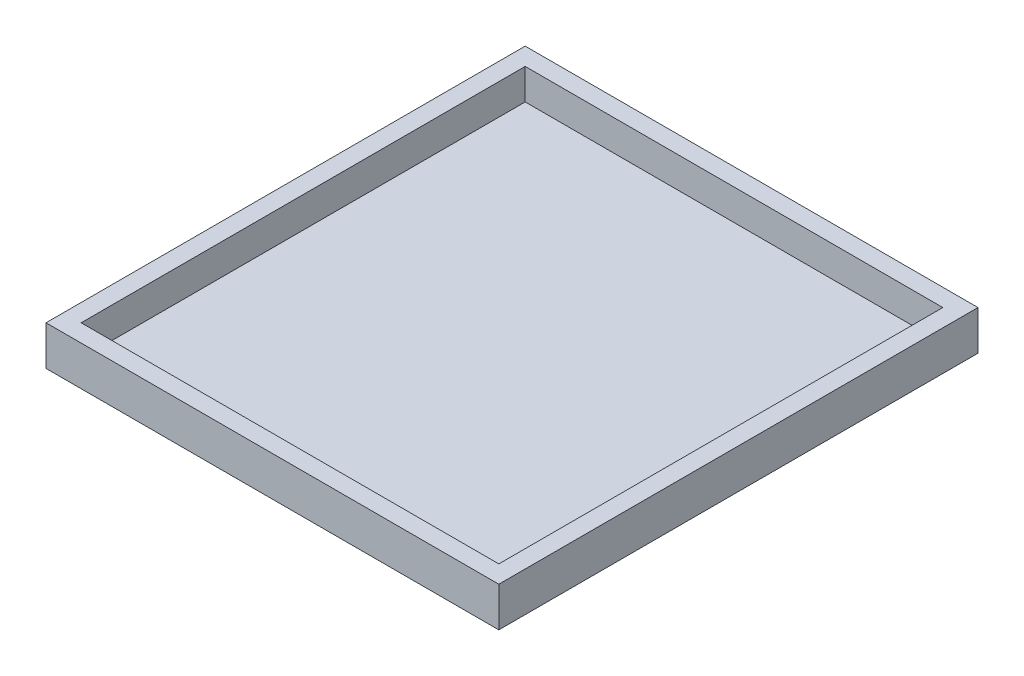
SolidWorks part; units mm, degrees
ref_plane "Front Plane" through (0, 0, 0) normal (0, 0, 1) x (1, 0, 0)
ref_plane "Top Plane" through (0, 0, 0) normal (0, 1, 0) x (1, 0, 0)
ref_plane "Right Plane" through (0, 0, 0) normal (1, 0, 0) x (0, 0, -1)
sketch "Sketch1" plane through (0, 0, 0) normal (0, 1, 0) x (1, 0, 0)
  line L1 (-47.5, 35.7063) -> (47.5, 35.7063)
  line L2 (-47.5, 35.7063) -> (-47.5, -65.2937)
  line L3 (-47.5, -65.2937) -> (47.5, -65.2937)
  line L4 (47.5, 35.7063) -> (47.5, -65.2937)
  line L5 (-47.5, 35.7063) -> (47.5, -65.2937) construction
  line L6 (-47.5, -65.2937) -> (47.5, 35.7063) construction
  point P0 (0, -14.7937)
  dimension "D1" = 95
  dimension "D2" = 101
extrude "Boss-Extrude1" add sketch "Sketch1" along normal blind 2
sketch "Sketch2" plane through (0, 2, 0) normal (0, 1, 0) x (1, 0, 0)
  line L8 (51.5, -69.2937) -> (51.5, 39.7063)
  line L9 (51.5, 39.7063) -> (-51.5, 39.7063)
  line L10 (-51.5, 39.7063) -> (-51.5, -69.2937)
  line L11 (-51.5, -69.2937) -> (51.5, -69.2937)
  line L12 (51.5, -69.2937) -> (51.5, 39.7063)
  line L13 (51.5, 39.7063) -> (-51.5, 39.7063)
  line L14 (-51.5, 39.7063) -> (-51.5, -69.2937)
  line L15 (-51.5, -69.2937) -> (51.5, -69.2937)
  dimension "D1" = 4
extrude "Boss-Extrude2" add sketch "Sketch2" along normal blind 7
sketch "Sketch3" plane through (0, 9, 0) normal (0, 1, 0) x (1, 0, 0)
  line L0 (-51.5, 39.7063) -> (51.5, -69.2937)
  line L2 (-47.5, 35.7063) -> (47.5, 35.7063)
  line L3 (-47.5, 35.7063) -> (-47.5, -65.2937)
  line L4 (-47.5, -65.2937) -> (47.5, -65.2937)
  line L5 (47.5, 35.7063) -> (47.5, -65.2937)
  line L6 (-47.5, 35.7063) -> (47.5, -65.2937) construction
  line L7 (-47.5, -65.2937) -> (47.5, 35.7063) construction
  point P5 (0, -14.7937)
  dimension "D1" = 101
  dimension "D2" = 95
extrude "Cut-Extrude1" cut sketch "Sketch3" against normal blind 7 contours L5 L0 L3 L4 | L5 L2 L3 L0
sketch "Sketch4" plane through (0, 2, 0) normal (0, -1, 0) x (1, 0, 0)
  line L1 (51.5, -39.7063) -> (-51.5, -39.7063)
  line L2 (51.5, -39.7063) -> (51.5, 69.2937)
  line L3 (51.5, 69.2937) -> (-51.5, 69.2937)
  line L4 (-51.5, -39.7063) -> (-51.5, 69.2937)
extrude "Boss-Extrude9" add sketch "Sketch4" along normal through all
sketch3d "3DSketch1"
  line L0 (49.5, 9, 67.2937) -> (49.5, 9, -37.7063)
  line L1 (49.5, 9, -37.7063) -> (-49.5, 9, -37.7063)
  line L2 (-49.5, 9, -37.7063) -> (-49.5, 9, 67.2937)
  line L3 (-49.5, 9, 67.2937) -> (49.5, 9, 67.2937)
  line L4 (49.5, 9, 67.2937) -> (49.5, 9, -37.7063)
  line L5 (49.5, 9, -37.7063) -> (-49.5, 9, -37.7063)
  line L6 (-49.5, 9, -37.7063) -> (-49.5, 9, 67.2937)
  line L7 (-49.5, 9, 67.2937) -> (49.5, 9, 67.2937)
  dimension "D1" = 2
